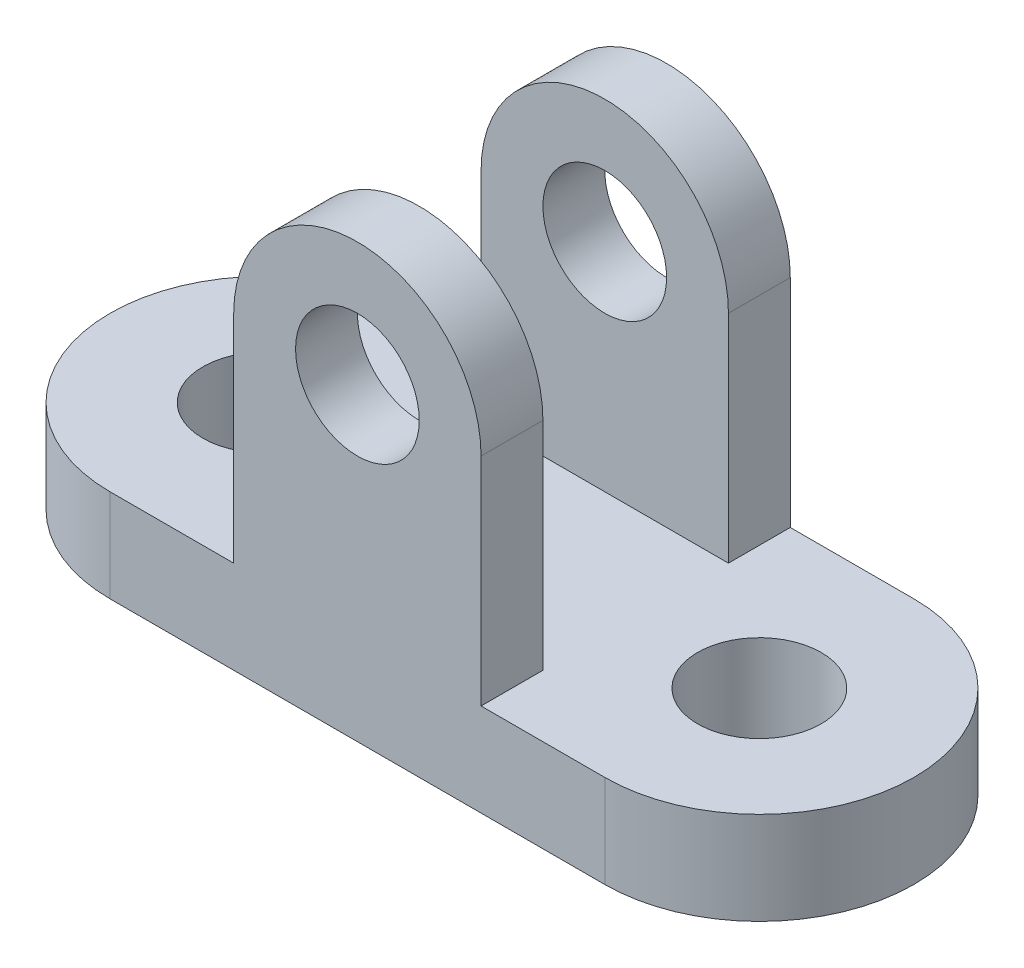
SolidWorks part; units mm, degrees
ref_plane "Front Plane" through (0, 0, 0) normal (0, 0, 1) x (1, 0, 0)
ref_plane "Top Plane" through (0, 0, 0) normal (0, 1, 0) x (1, 0, 0)
ref_plane "Right Plane" through (0, 0, 0) normal (1, 0, 0) x (0, 0, -1)
sketch "Sketch1" plane through (0, 0, 0) normal (0, 1, 0) x (1, 0, 0)
  line L0 (0, 0) -> (80, 0) construction
  line L1 (0, 25) -> (80, 25)
  line L2 (0, -25) -> (80, -25)
  arc A0 (0, 25) -> (0, -25) centre (0, 0) ccw
  arc A1 (80, -25) -> (80, 25) centre (80, 0) ccw
  point P3 (40, 0)
  dimension "D1" = 25
  dimension "D2" = 80
extrude "Boss-Extrude1" add sketch "Sketch1" along normal blind 15
sketch "Sketch2" plane through (0, 15, 0) normal (0, 1, 0) x (1, 0, 0)
  line L0 (40, 42.6912) -> (40, -48.6205) construction
  circle A0 centre (0, 0) radius 10
  circle A1 centre (80, 0) radius 10
  dimension "D1" = 20
  dimension "D2" = 80
extrude "Cut-Extrude1" cut sketch "Sketch2" against normal through all
sketch "Sketch3" plane through (0, 15, 0) normal (0, 1, 0) x (1, 0, 0)
  line L0 (80, 25) -> (0, 25) construction
  line L1 (20, 25) -> (60, 25)
  line L2 (20, 25) -> (20, 15)
  line L3 (20, 15) -> (60, 15)
  line L4 (60, 25) -> (60, 15)
  line L5 (-35.599, 0) -> (114.0178, 0) construction
  line L6 (20, -15) -> (60, -15)
  line L7 (60, -25) -> (60, -15)
  line L8 (20, -25) -> (60, -25)
  line L9 (20, -25) -> (20, -15)
  point P8 (60, 20)
  dimension "D1" = 20
  dimension "D2" = 40
  dimension "D3" = 10
extrude "Boss-Extrude2" add sketch "Sketch3" along normal blind 55
sketch "Sketch4" plane through (0, 0, 25) normal (0, 0, 1) x (1, 0, 0)
  line L0 (20, 70) -> (20, 15) construction
  line L1 (20, 70) -> (60, 70) construction
  line L2 (-8.5217, 50) -> (80.023, 50) construction
  line L3 (20, 50) -> (20, 70)
  line L4 (20, 70) -> (60, 70)
  line L5 (60, 70) -> (60, 50)
  arc A0 (60, 50) -> (20, 50) centre (40, 50) ccw
  circle A1 centre (40, 50) radius 10
  point P14 (0, 0)
  point P15 (0, 0)
  line M6 (60, 15) -> (60, 70)
  line M7 (60, 70) -> (20, 70)
  line M8 (20, 70) -> (20, 15)
  dimension "D1" = 40
  dimension "D2" = 20
extrude "Cut-Extrude2" cut sketch "Sketch4" against normal through all both and the other way through all contours A1 L2 | L2 A1 | A0 M6 M7 | A0 L4 M8
